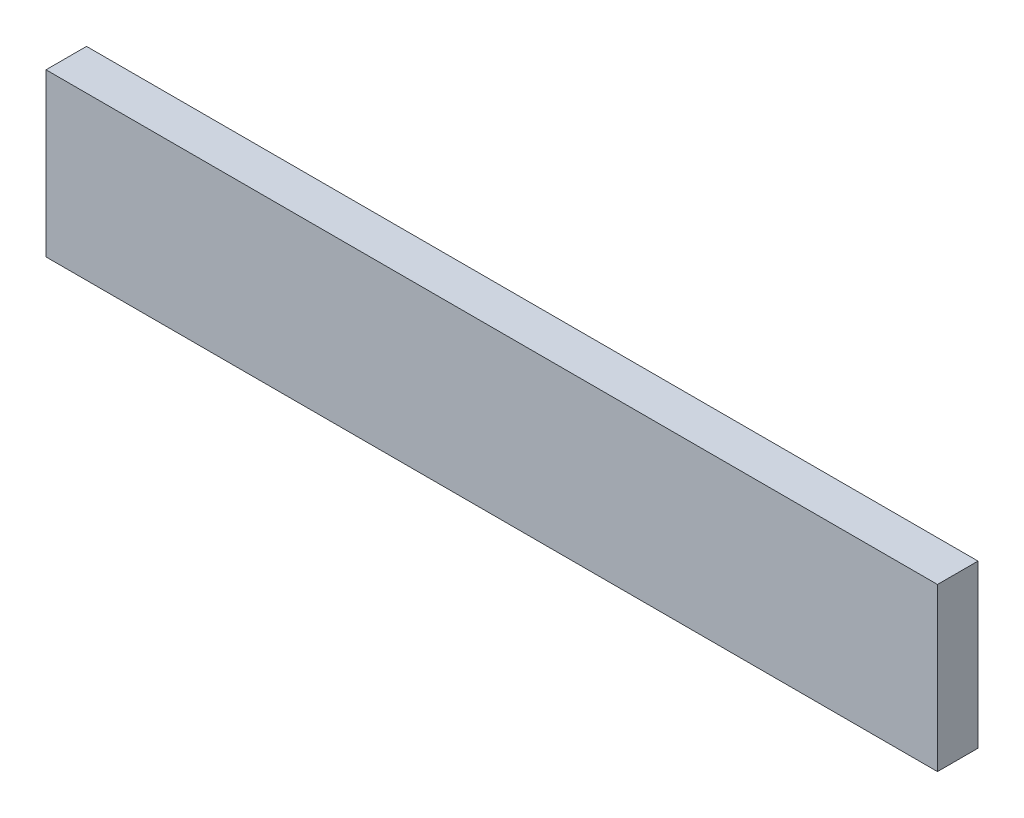
SolidWorks part; units mm, degrees
material "Plain Carbon Steel"
ref_plane "Front Plane" through (0, 0, 0) normal (0, 0, 1) x (1, 0, 0)
ref_plane "Top Plane" through (0, 0, 0) normal (0, 1, 0) x (1, 0, 0)
ref_plane "Right Plane" through (0, 0, 0) normal (1, 0, 0) x (0, 0, -1)
sketch "Sketch1" plane through (0, 0, 0) normal (0, 0, 1) x (1, 0, 0)
  line L1 (0, 0) -> (69.85, 0)
  line L2 (0, 0) -> (0, 12.7)
  line L3 (0, 12.7) -> (69.85, 12.7)
  line L4 (69.85, 0) -> (69.85, 12.7)
  dimension "D1" = 69.85
  dimension "D2" = 12.7
extrude "Boss-Extrude1" add sketch "Sketch1" along normal blind 3.175
